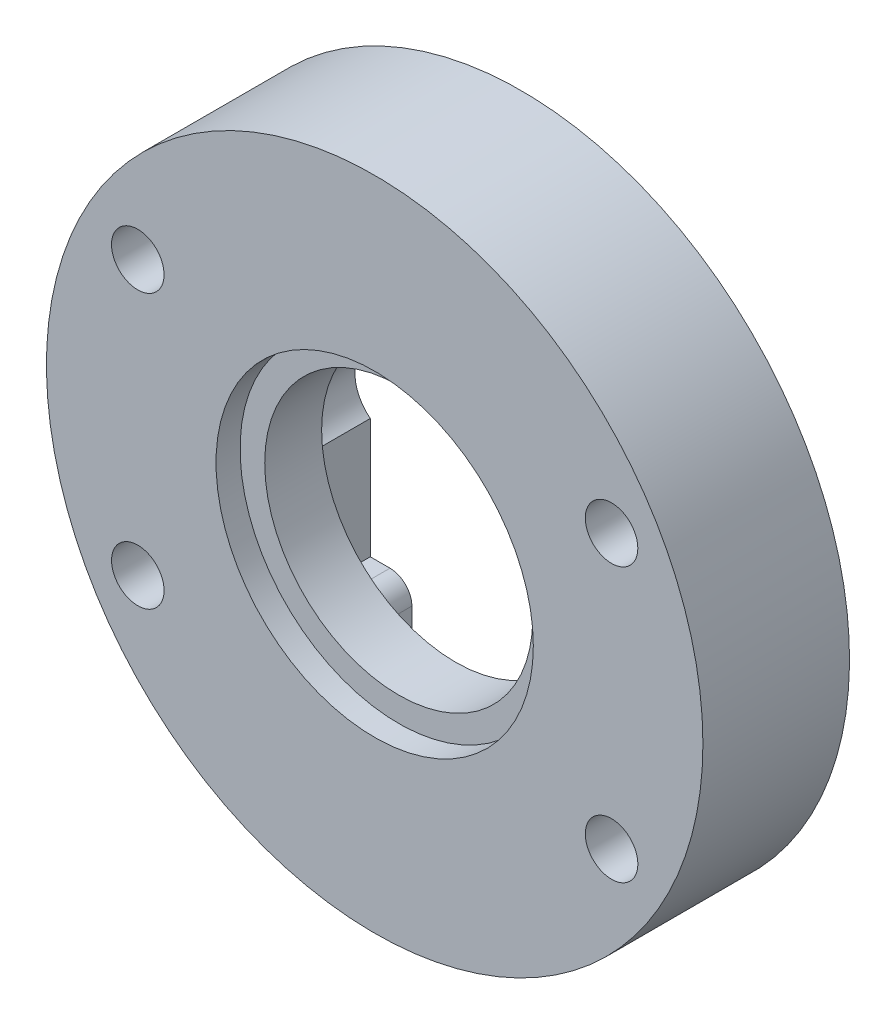
SolidWorks part; units mm, degrees
ref_plane "정면" through (0, 0, 0) normal (0, 0, 1) x (1, 0, 0)
ref_plane "윗면" through (0, 0, 0) normal (0, 1, 0) x (1, 0, 0)
ref_plane "우측면" through (0, 0, 0) normal (1, 0, 0) x (0, 0, -1)
sketch "스케치1" plane through (0, 0, 0) normal (0, 0, 1) x (1, 0, 0)
  line L0 (-5, -6.9) -> (-6.9, -6.9)
  line L2 (-5, -6.9) -> (-5, -14.1421)
  line L3 (0, -6.9) -> (0, -15) construction
  line L4 (5, -6.9) -> (5, -14.1421)
  line L6 (6.9, -6.9) -> (5, -6.9)
  line L7 (6.9, -6.9) -> (6.9, 6.9)
  line L8 (6.9, 6.9) -> (-6.9, 6.9)
  line L9 (-6.9, -6.9) -> (-6.9, 6.9)
  arc A0 (5, -14.1421) -> (-5, -14.1421) centre (0, 0) ccw
  circle A2 centre (0, 9.5) radius 2.1 construction
  circle A3 centre (0, 0) radius 9.5 construction
  point P1 (0, 6.9)
  point P15 (6.9, 0)
  point P19 (0, 0)
  point P28 (0, 0)
  dimension "D1" = 30
  dimension "D2" = 4.2
  dimension "D6" = 13.8
  dimension "D7" = 5
  dimension "D8" = 13.8
  dimension "D3" = 19
extrude "보스-돌출1" add sketch "스케치1" along normal blind 3
sketch "스케치11" plane through (0, 0, 3) normal (0, 0, 1) x (1, 0, 0)
  line L0 (5.8, 0) -> (-5.8, 0) construction
  line L1 (5.8, 0) -> (-5.8, 0) construction
  line L2 (5.8, -1.8) -> (-5.8, -1.8)
  line L3 (5.8, 1.8) -> (-5.8, 1.8)
  arc A0 (5.8, -1.8) -> (5.8, 1.8) centre (5.8, 0) ccw
  arc A1 (-5.8, 1.8) -> (-5.8, -1.8) centre (-5.8, 0) ccw
  point P4 (0, 0)
  point P6 (0, 0)
  dimension "D2" = 1.8
  dimension "D1" = 11.6
extrude "컷-돌출4" cut sketch "스케치11" against normal through all
sketch "스케치12" plane through (0, 0, 3) normal (0, 0, 1) x (1, 0, 0)
  circle A0 centre (0, 0) radius 15
  circle A1 centre (0, 0) radius 6.125
  dimension "D1" = 30
  dimension "D2" = 12.25
extrude "보스-돌출2" add sketch "스케치12" along normal blind 2.6
sketch "스케치13" plane through (0, 0, 5.6) normal (0, 0, 1) x (1, 0, 0)
  circle A0 centre (0, 0) radius 7.25
  circle A1 centre (0, 0) radius 15
  dimension "D1" = 14.5
  dimension "D2" = 30
extrude "보스-돌출3" add sketch "스케치13" along normal blind 1.1
sketch "스케치14" plane through (0, 0, 6.7) normal (0, 0, 1) x (1, 0, 0)
  line L0 (0, 0) -> (15, 0) construction
  line L1 (0, 0) -> (0, 15) construction
  line L2 (0, 0) -> (10.8253, 6.25) construction
  circle A0 centre (0, 0) radius 15 construction
  circle A1 centre (10.8253, 6.25) radius 1.2
  circle A2 centre (-10.8253, 6.25) radius 1.2
  circle A3 centre (10.8253, -6.25) radius 1.2
  circle A4 centre (-10.8253, -6.25) radius 1.2
  dimension "D1" = 2.4
  dimension "D2" = 12.5
  dimension "D3" = 60
extrude "컷-돌출5" cut sketch "스케치14" against normal through all
fillet "필렛1" radius 1 2 edges at (-5, -6.9, 1.5) (5, -6.9, 1.5)
